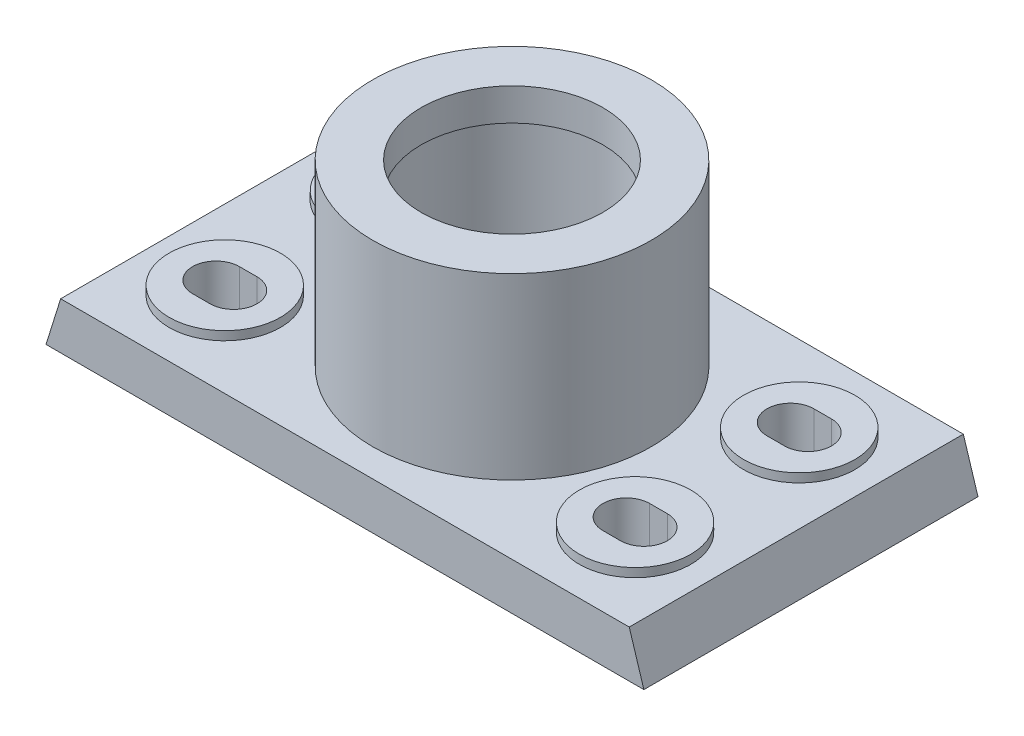
SolidWorks part; units mm, degrees
ref_plane "Front Plane" through (0, 0, 0) normal (0, 0, 1) x (1, 0, 0)
ref_plane "Top Plane" through (0, 0, 0) normal (0, 1, 0) x (1, 0, 0)
ref_plane "Right Plane" through (0, 0, 0) normal (1, 0, 0) x (0, 0, -1)
sketch "Sketch1" plane through (0, 0, 0) normal (0, 0, 1) x (1, 0, 0)
  line L0 (-102, 0) -> (102, 0)
  line L1 (-102, 0) -> (-97, 16)
  line L2 (0, 195.3499) -> (0, -75.2319) construction
  line L3 (-97, 16) -> (97, 16)
  line L4 (102, 0) -> (97, 16)
  line L5 (-145.7574, 16) -> (141.5074, 16) construction
  point P6 (0, 0)
  dimension "D1" = 16
  dimension "D2" = 5
  dimension "D3" = 16
  dimension "D4" = 5
  dimension "D5" = 204
extrude "Boss-Extrude1" add sketch "Sketch1" along normal mid plane 114
sketch "Sketch2" plane through (0, 0, 0) normal (0, -1, 0) x (1, 0, 0)
  line L0 (-102, -57) -> (102, -57) construction
  line L1 (-92, 47) -> (-6.5, 47)
  line L2 (-92, 47) -> (-92, -47)
  line L3 (-92, -47) -> (-6.5, -47)
  line L4 (-6.5, 47) -> (-6.5, -47)
  line L5 (-102, 57) -> (-102, -57) construction
  dimension "D1" = 85.5
  dimension "D2" = 94
  dimension "D3" = 10
  dimension "D4" = 10
extrude "Cut-Extrude1" cut sketch "Sketch2" against normal blind 3
mirror "Mirror1" about plane through (0, 0, 0) normal (1, 0, 0) of "Cut-Extrude1"
sketch "Sketch4" plane through (0, 16, 0) normal (0, 1, 0) x (1, 0, 0)
  circle A0 centre (0, 0) radius 47.5
  dimension "D1" = 95
extrude "Boss-Extrude2" add sketch "Sketch4" along normal blind 61
sketch "Sketch6" plane through (0, 16, 0) normal (0, 1, 0) x (1, 0, 0)
  line L0 (97, -57) -> (-97, -57) construction
  circle A0 centre (70, -28) radius 19
  circle A1 centre (70, 28) radius 19
  dimension "D1" = 29
  dimension "D3" = 56
  dimension "D4" = 38
  dimension "D2" = 70
extrude "Boss-Extrude4" add sketch "Sketch6" along normal blind 3
sketch "Sketch9" plane through (0, 19, 0) normal (0, 1, 0) x (1, 0, 0)
  line L0 (73, -28) -> (67, -28) construction
  line L1 (73, -36) -> (67, -36)
  line L2 (73, -20) -> (67, -20)
  arc A0 (73, -36) -> (73, -20) centre (73, -28) ccw
  arc A1 (67, -20) -> (67, -36) centre (67, -28) ccw
  point P2 (70, -28)
  dimension "D3" = 22
  dimension "D1" = 70
  dimension "D2" = 16
  dimension "D4" = 28
extrude "Cut-Extrude2" cut sketch "Sketch9" against normal through all
mirror "Mirror2" about plane through (0, 0, 0) normal (1, 0, 0) of "Boss-Extrude4"
mirror "Mirror3" about plane through (0, 0, 0) normal (0, 0, 1) of "Cut-Extrude2"
mirror "Mirror4" about plane through (0, 0, 0) normal (1, 0, 0) of "Mirror3", "Cut-Extrude2"
sketch "Sketch10" plane through (0, 77, 0) normal (0, 1, 0) x (1, 0, 0)
  circle A0 centre (0, 0) radius 31
  dimension "D1" = 62
extrude "Cut-Extrude3" cut sketch "Sketch10" against normal blind 11
sketch "Sketch11" plane through (0, 66, 0) normal (0, 1, 0) x (1, 0, 0)
  circle A0 centre (0, 0) radius 32.5
  dimension "D1" = 65
extrude "Cut-Extrude4" cut sketch "Sketch11" against normal blind 37
sketch "Sketch12" plane through (0, 29, 0) normal (0, 1, 0) x (1, 0, 0)
  circle A0 centre (0, 0) radius 31
  dimension "D1" = 62
extrude "Cut-Extrude5" cut sketch "Sketch12" against normal blind 13
sketch "Sketch13" plane through (0, 16, 0) normal (0, 1, 0) x (1, 0, 0)
  circle A0 centre (22, 0) radius 1.5
  dimension "D1" = 22
  dimension "D2" = 3
extrude "Cut-Extrude6" cut sketch "Sketch13" against normal blind 5
